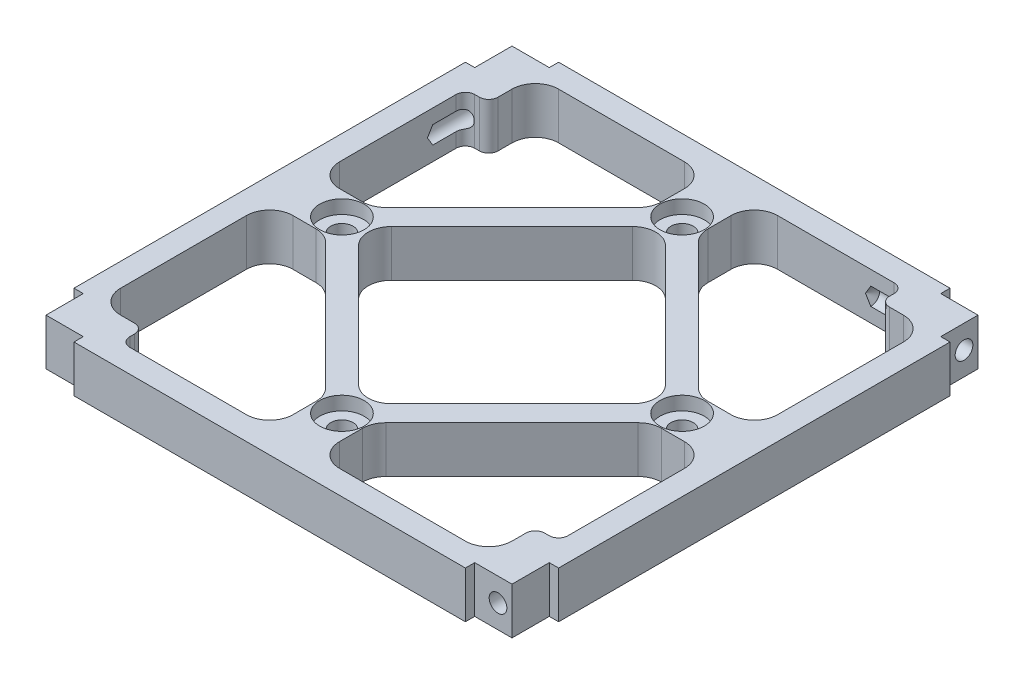
SolidWorks part; units mm, degrees
material "6061-T6 (SS)"
ref_plane "Front Plane" through (0, 0, 0) normal (0, 0, 1) x (1, 0, 0)
ref_plane "Top Plane" through (0, 0, 0) normal (0, 1, 0) x (1, 0, 0)
ref_plane "Right Plane" through (0, 0, 0) normal (1, 0, 0) x (0, 0, -1)
sketch "Sketch1" plane through (0, 0, 0) normal (0, 1, 0) x (1, 0, 0)
  line L0 (-42, 47) -> (-42, 37)
  line L1 (-52, 52) -> (52, 52)
  line L2 (-52, 52) -> (-52, -52)
  line L3 (-52, -52) -> (52, -52)
  line L4 (52, 52) -> (52, -52)
  line L5 (-47, 5) -> (-35, 5)
  line L6 (-35, 5) -> (-5, 35)
  line L7 (-5, 35) -> (-5, 47)
  line L8 (-5, 47) -> (-42, 47)
  line L9 (0, 0) -> (0, 76.3292) construction
  line L10 (0, 0) -> (-78.8537, 0) construction
  line L11 (0, 0) -> (-66.7994, 66.7994) construction
  line L12 (-32.9289, 0) -> (0, 32.9289)
  line L13 (0, 32.9289) -> (32.9289, 0)
  line L14 (32.9289, 0) -> (0, -32.9289)
  line L15 (0, -32.9289) -> (-32.9289, 0)
  line L16 (5, 47) -> (5, 35)
  line L17 (37, 47) -> (5, 47)
  line L18 (37, 42) -> (37, 47)
  line L19 (47, 42) -> (37, 42)
  line L20 (47, 5) -> (47, 42)
  line L21 (35, 5) -> (47, 5)
  line L22 (5, 35) -> (35, 5)
  line L23 (47, -5) -> (35, -5)
  line L24 (47, -37) -> (47, -5)
  line L25 (42, -37) -> (47, -37)
  line L26 (42, -47) -> (42, -37)
  line L27 (5, -47) -> (42, -47)
  line L28 (5, -35) -> (5, -47)
  line L29 (35, -5) -> (5, -35)
  line L30 (-5, -47) -> (-5, -35)
  line L31 (-42, 37) -> (-47, 37)
  line L32 (-47, 37) -> (-47, 5)
  line L33 (-37, -47) -> (-5, -47)
  line L34 (-37, -42) -> (-37, -47)
  line L35 (-47, -42) -> (-37, -42)
  line L36 (-47, -5) -> (-47, -42)
  line L37 (-35, -5) -> (-47, -5)
  line L38 (-5, -35) -> (-35, -5)
  point P36 (0.1996, 0.1996)
  point P45 (0, 0)
  dimension "D1" = 104
  dimension "D2" = 5
  dimension "D3" = 5
  dimension "D4" = 5
  dimension "D5" = 5
  dimension "D6" = 5
  dimension "D7" = 12
  dimension "D8" = 10
  dimension "D9" = 10
  dimension "D10" = 4
extrude "Boss-Extrude1" add sketch "Sketch1" along normal blind 10
fillet "Fillet1" radius 5 24 edges at (32.9289, 5, 0) (0, 5, 32.9289) (-32.9289, 5, 0) (0, 5, -32.9289) (-5, 5, -47) (-5, 5, -35) (-35, 5, -5) (-47, 5, 42) (-47, 5, 5) (-35, 5, 5) (-5, 5, 35) (-5, 5, 47) (42, 5, 47) (47, 5, 5) (35, 5, 5) (5, 5, 35) (5, 5, 47) (47, 5, -42) (47, 5, -5) (35, 5, -5) (5, 5, -35) (5, 5, -47) (-42, 5, -47) (-47, 5, -5)
sketch "Sketch2" plane through (0, 10, 0) normal (0, 1, 0) x (1, 0, 0)
  line L0 (-52, 52) -> (-42, 52)
  line L1 (52, 52) -> (-52, 52) construction
  line L2 (-42, 52) -> (-42, 50)
  line L3 (-42, 50) -> (-50, 50)
  line L4 (-50, 50) -> (-50, 42)
  line L5 (-50, 42) -> (-52, 42)
  line L6 (-52, 52) -> (-52, -52) construction
  line L7 (-52, 42) -> (-52, 52)
  dimension "D1" = 2
  dimension "D2" = 10
extrude "Cut-Extrude1" cut sketch "Sketch2" against normal through all
ref_axis "Axis1" through (0, 10.5, 0) along (0, -1, 0)
pattern_circular "CirPattern1" count 4 over 360 about axis through (0, 0, 0) along (0, 1, 0) of "Cut-Extrude1"
hole_wizard "CBORE for #12 Binding Head Machine Screw1" positions "Sketch3" profile "Sketch5" counterbore size "#12" standard "ANSI Inch" end condition through all
sketch "Sketch3" plane through (0, 10, 0) normal (0, 1, 0) x (1, 0, 0)
  line L2 (0, 36.5) -> (36.5, 0)
  line L3 (-36.5, 0) -> (0, -36.5)
  line L4 (36.5, 0) -> (0, -36.5)
  line L6 (0, 0) -> (0, 48.9753) construction
  line L7 (0, 0) -> (-18.2924, 0) construction
  line L9 (-36.5, 0) -> (0, 36.5)
  line L11 (-3.5355, 29.3934) -> (-29.3934, 3.5355) construction
  point P0 (0, 36.5)
  point P199 (-36.5, 0)
  point P315 (0, -36.5)
  point P316 (36.5, 0)
  dimension "D1" = 36.5
sketch "Sketch5" plane through (0, 10, -36.5) normal (1, 0, 0) x (0, 0, 1)
  line L0 (0, 0) -> (0, 10)
  line L1 (0, 10) -> (2.4003, 10)
  line L3 (2.4003, 10) -> (2.4003, 2.921)
  line L4 (2.4003, 2.921) -> (4.7625, 2.921)
  line L5 (4.7625, 2.921) -> (4.7625, 0)
  line L7 (4.7625, 0) -> (0, 0)
  line L11 (0, -6.35) -> (0, 107.95) construction
  dimension "Thru Hole Dia." = 4.8006
  dimension "Thru Hole Depth" = 10
  dimension "C'Bore Dia." = 9.525
  dimension "C'Bore Depth" = 2.921
fillet "Fillet3" radius 2 8 edges at (-37, 5, 42) (-37, 5, 47) (42, 5, 37) (47, 5, 37) (37, 5, -42) (37, 5, -47) (-47, 5, -37) (-42, 5, -37)
hole_wizard "#10-24 Tapped Hole1" positions "Sketch6" profile "Sketch9" tap size "#10-24" standard "ANSI Inch"
sketch "Sketch6" plane through (50, 0, 0) normal (1, 0, 0) x (0, 0, -1)
  line L2 (42, 10) -> (52, 0)
  point P0 (47, 5)
  point P13 (47, 5)
sketch "Sketch9" plane through (50, 5, -47) normal (0, 1, 0) x (0, 0, -1)
  line L0 (0, 0) -> (0, 21.1408)
  line L1 (0, 21.1408) -> (1.8986, 20)
  line L2 (1.8986, 20) -> (1.8986, 0)
  line L5 (1.8986, 0) -> (0, 0)
  line L10 (0, 21.1408) -> (-1.8987, 20) construction
  line L11 (0, -6.35) -> (0, 107.95) construction
  dimension "Tap Drill Dia." = 3.7973
  dimension "Tap Drill Depth" = 20
  dimension "Drill Angle" = 118
cosmetic thread "Hole Thread1" parameters "D1"=9.65, "D2"=4.826
pattern_circular "CirPattern5" count 4 over 360 about axis through (0, 10.5, 0) along (0, -1, 0) of "#10-24 Tapped Hole1"
